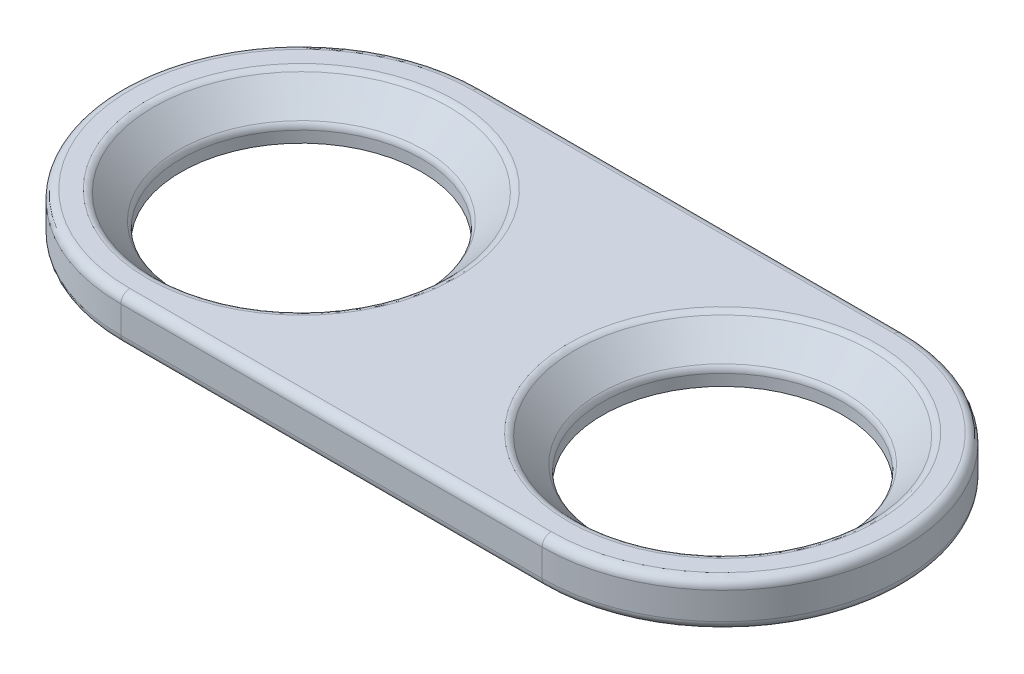
SolidWorks part; units mm, degrees
ref_plane "Front Plane" through (0, 0, 0) normal (0, 0, 1) x (1, 0, 0)
ref_plane "Top Plane" through (0, 0, 0) normal (0, 1, 0) x (1, 0, 0)
ref_plane "Right Plane" through (0, 0, 0) normal (1, 0, 0) x (0, 0, -1)
sketch "Sketch1" plane through (0, 0, 0) normal (0, 1, 0) x (1, 0, 0)
  line L0 (-102.3855, 0) -> (102.3855, 0) construction
  line L1 (-7, 6) -> (7, 6)
  line L2 (0, -26.3097) -> (0, 26.3097) construction
  line L3 (7, -6) -> (-7, -6)
  arc A0 (-7, 6) -> (-7, -6) centre (-7, 0) ccw
  arc A1 (7, -6) -> (7, 6) centre (7, 0) ccw
  point P1 (0, 6)
  dimension "D1" = 6
  dimension "D2" = 14
extrude "Boss-Extrude1" add sketch "Sketch1" along normal blind 1.5
sketch "Sketch2" plane through (0, 0, 0) normal (0, 1, 0) x (1, 0, 0)
  circle A0 centre (-7, 0) radius 4
  circle A1 centre (7, 0) radius 4
  dimension "D1" = 8
extrude "Cut-Extrude2" cut sketch "Sketch2" along normal through all
chamfer "Chamfer1" distance 1 angle 45 2 edges at (-7, 1.5, 4) (7, 1.5, 4)
fillet "Fillet1" radius 0.3 12 edges at (7, 0.5, 4) (-7, 0.5, 4) (7, 1.5, 5) (-7, 1.5, 5) (0, 0, -6) (13, 0, 0) (0, 0, 6) (-13, 1.5, 0) (0, 1.5, -6) (13, 1.5, 0) (-13, 0, 0) (0, 1.5, 6)
